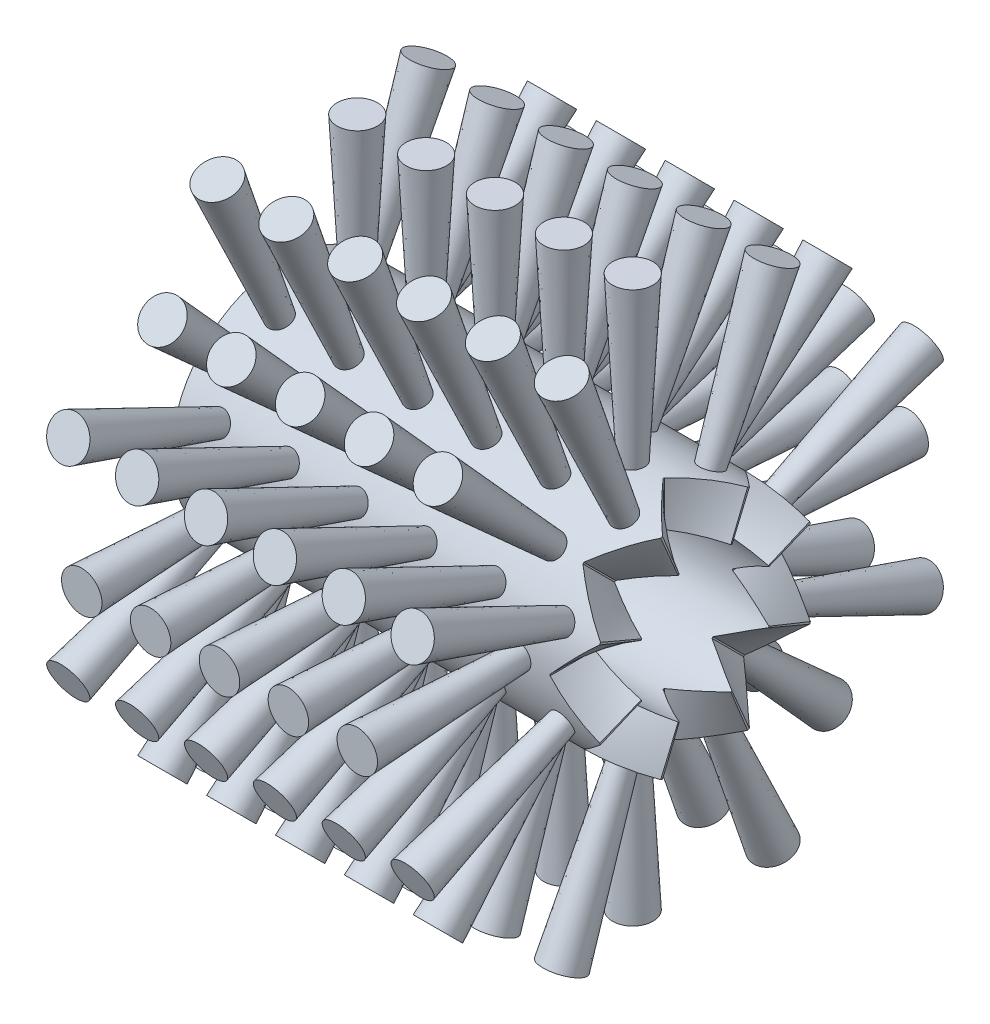
SolidWorks part; units mm, degrees
material "PA6"
ref_plane "Vorderansicht" through (0, 0, 0) normal (0, 0, 1) x (1, 0, 0)
ref_plane "Draufsicht" through (0, 0, 0) normal (0, 1, 0) x (1, 0, 0)
ref_plane "Seitenansicht" through (0, 0, 0) normal (1, 0, 0) x (0, 0, -1)
sketch "Skizze1" plane through (0, 0, 0) normal (1, 0, 0) x (0, 0, -1)
  circle A0 centre (0, 0) radius 10
  circle A1 centre (0, 0) radius 16.5
  dimension "D1" = 20
  dimension "D2" = 33
extrude "Linear austragen1" add sketch "Skizze1" along normal blind 61
ref_plane "Ebene1" through (30.5, 16.5, 0) normal (0, 1, 0) x (0, 0, -1)
sketch "Skizze3" plane through (61, 0, 0) normal (1, 0, 0) x (0, 0, -1)
  line L0 (0, 0) -> (-6.6664, 16.5) construction
  line L1 (-6.6664, 16.5) -> (6.6664, 16.5) construction
  line L2 (6.6664, 16.5) -> (0, 0) construction
  line L3 (0, 20.4486) -> (0, -20.4486) construction
  line L4 (-3.2322, 8) -> (3.2322, 8) construction
  line L5 (18.8494, 0) -> (-18.8494, 0) construction
  circle A0 centre (0, 0) radius 16.5 construction
  point P4 (0, 16.5)
  dimension "D1" = 44
sketch "Skizze4" plane through (30.5, 16.5, 0) normal (0, 1, 0) x (0, 0, -1)
  line L0 (6.6664, -30.5) -> (0.1, -24.5)
  line L1 (0.1, -24.5) -> (-0.1, -24.5)
  line L2 (-0.1, -24.5) -> (-6.6664, -30.5)
  line L3 (-6.6664, -30.5) -> (6.6664, -30.5)
  line L4 (0, 50.9486) -> (0, 10.0514) construction
  point P6 (0, -24.5)
ref_plane "Ebene2" through (0, 8, 0) normal (0, 1, 0) x (-1, 0, 0)
sketch "Skizze5" plane through (0, 8, 0) normal (0, 1, 0) x (-1, 0, 0)
  line L0 (-61, 3.2322) -> (-55, 0.1)
  line L3 (-61, 0) -> (-61, 6.6664) construction
  line L5 (-55, 0.1) -> (-55, -0.1)
  line L6 (-55, -0.1) -> (-61, -3.2322)
  line L8 (-61, 3.2322) -> (-61, -3.2322)
  line L10 (20.4486, 0) -> (-20.4486, 0) construction
  point P4 (-55, 0)
loft "Schnitt-Ausformung1" cut profiles "Skizze5", "Skizze4"
pattern_circular "Kreismuster1" count 8 over 360 about axis through (61, 0, 0) along (-1, 0, 0) of "Schnitt-Ausformung1"
ref_plane "Ebene3" through (0, 0, 0) normal (0, -0.3827, 0.9239) x (1, 0, 0)
ref_plane "Ebene4" through (0, 14.5, 0) normal (0, 1, 0) x (-1, 0, 0)
sketch "Skizze8" plane through (0, 14.5, 0) normal (0, 1, 0) x (-1, 0, 0)
  line L0 (20.4486, 0) -> (-20.4486, 0) construction
  line L1 (-61, -3.7461) -> (-61, -6.181) construction
  circle A0 centre (-50.5, 0) radius 1.6
  dimension "D1" = 3.2
  dimension "D2" = 10.5
extrude "Bürste1" add sketch "Skizze8" along normal blind 25.5 draft 3 draft outward yes
ref_plane "Ebene5" through (30.5, 15.244, 6.3143) normal (0, 0.9239, 0.3827) x (0, 0.3827, -0.9239)
ref_plane "Ebene6" through (0, 13.3963, 5.5489) normal (0, 0.9239, 0.3827) x (-1, 0, 0)
sketch "Skizze9" plane through (0, 13.3963, 5.5489) normal (0, 0.9239, 0.3827) x (-1, 0, 0)
  line L0 (20.4486, 0) -> (-20.4486, 0) construction
  line L1 (-61, 0.144) -> (-61, -0.144) construction
  circle A0 centre (-55.5, 0) radius 1.6
  dimension "D1" = 3.2
  dimension "D2" = 5.5
extrude "Bürtse2" add sketch "Skizze9" along normal blind 25.5 draft 3 draft outward yes
pattern_circular "Kreismuster3" count 8 over 360 about axis through (0, 0, 0) along (1, 0, 0) of "Bürste1"
pattern_linear "Lineares Muster1" count 5 spacing 10 along (-1, 0, 0) of "Kreismuster3", "Bürste1"
pattern_circular "Kreismuster4" count 8 over 360 about axis through (0, 0, 0) along (1, 0, 0) of "Bürtse2"
pattern_linear "Lineares Muster2" count 6 spacing 10 along (-1, 0, 0) of "Kreismuster4", "Bürtse2"
